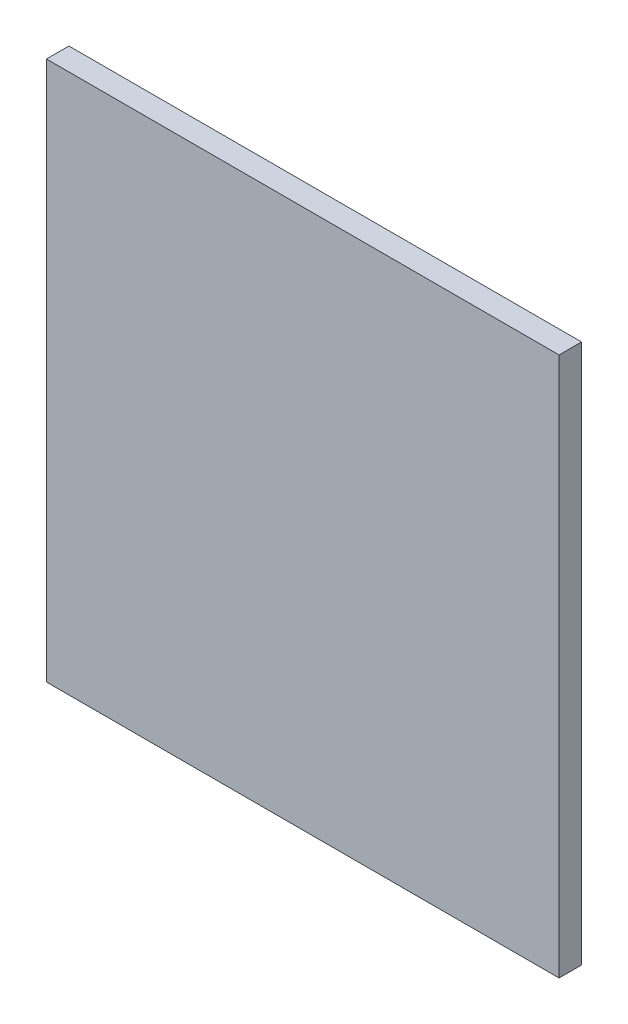
SolidWorks part; units mm, degrees
ref_plane "Front Plane" through (0, 0, 0) normal (0, 0, 1) x (1, 0, 0)
ref_plane "Top Plane" through (0, 0, 0) normal (0, 1, 0) x (1, 0, 0)
ref_plane "Right Plane" through (0, 0, 0) normal (1, 0, 0) x (0, 0, -1)
sketch "Sketch1" plane through (0, 0, 0) normal (0, 0, 1) x (1, 0, 0)
  line L1 (0, 0) -> (72.39, 0)
  line L2 (0, 0) -> (0, 76.2)
  line L3 (0, 76.2) -> (72.39, 76.2)
  line L4 (72.39, 0) -> (72.39, 76.2)
  dimension "D1" = 76.2
  dimension "D2" = 72.39
extrude "Boss-Extrude1" add sketch "Sketch1" along normal blind 3.175
